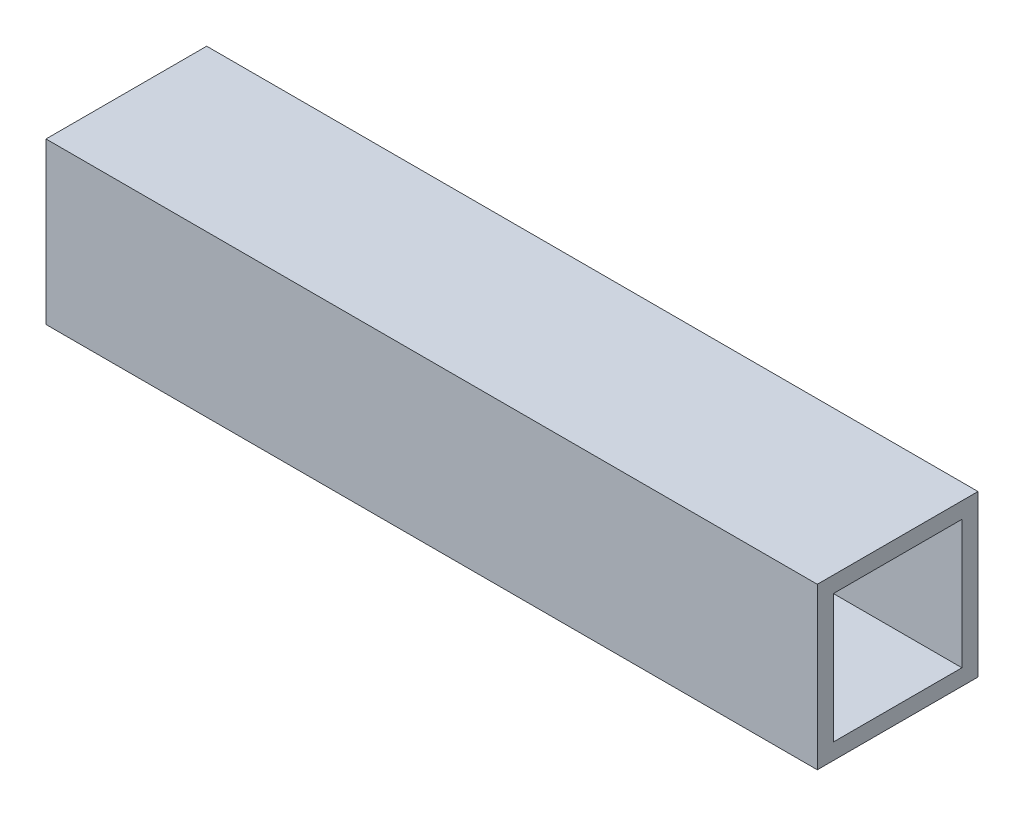
SolidWorks part; units mm, degrees
material "AISI 304"
ref_plane "Front Plane" through (0, 0, 0) normal (0, 0, 1) x (1, 0, 0)
ref_plane "Top Plane" through (0, 0, 0) normal (0, 1, 0) x (1, 0, 0)
ref_plane "Right Plane" through (0, 0, 0) normal (1, 0, 0) x (0, 0, -1)
sketch "Sketch1" plane through (0, 0, 0) normal (1, 0, 0) x (0, 0, -1)
  line L0 (31.75, -31.75) -> (31.75, 31.75)
  line L1 (-25.4, -25.4) -> (25.4, -25.4)
  line L2 (-25.4, -25.4) -> (-25.4, 25.4)
  line L3 (-25.4, 25.4) -> (25.4, 25.4)
  line L4 (25.4, -25.4) -> (25.4, 25.4)
  line L5 (-25.4, -25.4) -> (25.4, 25.4) construction
  line L6 (-25.4, 25.4) -> (25.4, -25.4) construction
  line L7 (-31.75, 31.75) -> (31.75, 31.75)
  line L8 (-31.75, -31.75) -> (-31.75, 31.75)
  line L9 (-31.75, -31.75) -> (31.75, -31.75)
  point P0 (0, 0)
  dimension "D1" = 50.8
  dimension "D2" = 50.8
  dimension "D3" = 6.35
extrude "Boss-Extrude1" add sketch "Sketch1" along normal mid plane 304.8
equation "\"D1@Sketch1\"=2in"
equation "\"D2@Sketch1\"=2in"
equation "\"D1@Boss-Extrude1\"=1ft"
